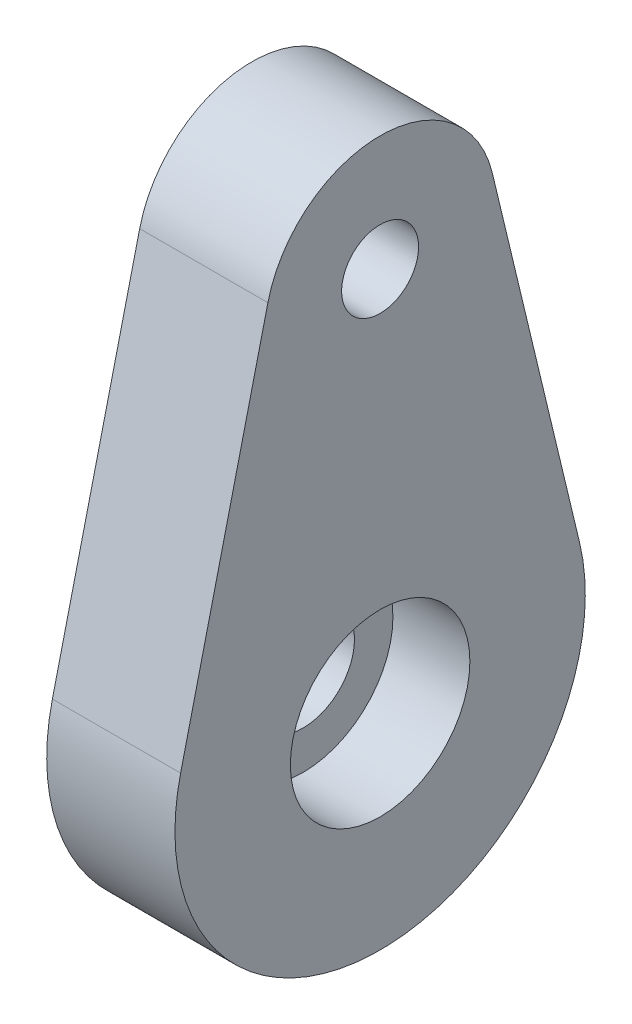
SolidWorks part; units mm, degrees
ref_plane "前视基准面" through (0, 0, 0) normal (0, 0, 1) x (1, 0, 0)
ref_plane "上视基准面" through (0, 0, 0) normal (0, 1, 0) x (1, 0, 0)
ref_plane "右视基准面" through (0, 0, 0) normal (1, 0, 0) x (0, 0, -1)
sketch "草图1" plane through (0, 0, 0) normal (1, 0, 0) x (0, 0, -1)
  line L0 (-7.7792, 1.8667) -> (-4.3758, 16.05)
  line L1 (0, 15) -> (0, 0) construction
  line L2 (4.3758, 16.05) -> (7.7792, 1.8667)
  arc A0 (4.3758, 16.05) -> (-4.3758, 16.05) centre (0, 15) ccw
  circle A1 centre (0, 0) radius 2
  arc A2 (-7.7792, 1.8667) -> (7.7792, 1.8667) centre (0, 0) ccw
  circle A3 centre (0, 15) radius 1.5
  dimension "D1" = 3
  dimension "D2" = 4
  dimension "D3" = 9
  dimension "D5" = 16
  dimension "D4" = 15
extrude "凸台-拉伸1" add sketch "草图1" along normal blind 5
sketch "草图2" plane through (0, 0, 0) normal (-1, 0, 0) x (0, 0, 1)
  circle A0 centre (0, 0) radius 3
  circle A1 centre (0, 0) radius 2 construction
  circle A2 centre (0, 0) radius 2
  dimension "D1" = 6
extrude "凸台-拉伸2" add sketch "草图2" along normal blind 0.5
sketch "草图3" plane through (5, 0, 0) normal (1, 0, 0) x (0, 0, -1)
  circle A0 centre (0, 0) radius 2 construction
  circle A1 centre (0, 0) radius 2
  circle A2 centre (0, 0) radius 3.5
  dimension "D1" = 7
extrude "切除-拉伸1" cut sketch "草图3" against normal blind 3
